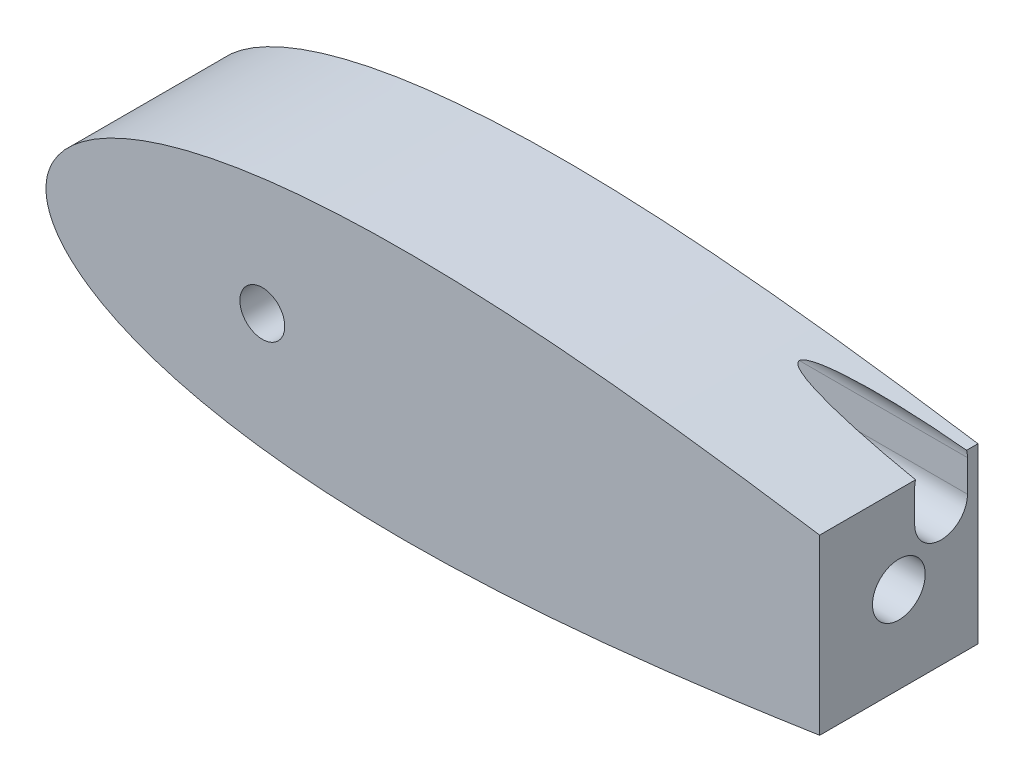
SolidWorks part; units mm, degrees
ref_plane "Front Plane" through (0, 0, 0) normal (0, 0, 1) x (1, 0, 0)
ref_plane "Top Plane" through (0, 0, 0) normal (0, 1, 0) x (1, 0, 0)
ref_plane "Right Plane" through (0, 0, 0) normal (1, 0, 0) x (0, 0, -1)
sketch "Sketch1" plane through (0, 0, 0) normal (0, 0, 1) x (1, 0, 0)
  line L0 (100, 0) -> (0, 0) construction
  line L1 (1.2169, -991.9959) -> (1.2169, 49008.0041) construction
  line L2 (93.345, 0) -> (114.935, 0) construction
  line L3 (125.634, 0) -> (131.6629, 0) construction
  line L4 (643.5991, 0) -> (643.5991, -1.016)
  line L9 (0, 0) -> (643.9668, 0)
  line L13 (460.661, 0) -> (473.361, 0)
  circle A0 centre (104.14, 0) radius 10.795 construction
  arc A1 (1.2169, -4.6585) -> (1.2169, 4.6585) centre (9.525, 0) cw
  arc A2 (641.5671, 0) -> (644.1071, 0) centre (642.8371, 0) ccw
  circle A4 centre (104.14, 0) radius 10.795
  circle A9 centre (40.64, 0) radius 12.7
  circle A14 centre (642.3793, 0) radius 1.5875 construction
  arc A15 (642.5108, -1.582) -> (642.5108, 1.582) centre (642.3793, 0) ccw
  spline S2 degree 3 poles (666.3448, -0.0547) (672.2538, 0) (666.3448, 0.0547) (662.8509, 0.2344) (656.505, 0.5436) (649.293, 1.0348) (640.4916, 1.7319) (630.4138, 2.6634) (619.0141, 3.8493) (606.375, 5.3044) (592.5439, 7.0376) (577.5855, 9.0506) (561.5643, 11.3389) (544.5497, 13.8907) (526.6141, 16.6877) (507.8326, 19.7051) (488.2827, 22.9117) (468.0444, 26.2704) (447.1994, 29.739) (425.8316, 33.2703) (404.0263, 36.8132) (381.8707, 40.3133) (359.4533, 43.7135) (336.8645, 46.9554) (314.1962, 49.9798) (291.5418, 52.7277) (268.9963, 55.1412) (246.6566, 57.1646) (224.6209, 58.7452) (202.9892, 59.8341) (181.8631, 60.3875) (161.3458, 60.367) (141.542, 59.7399) (122.5581, 58.4818) (104.5023, 56.5743) (87.485, 54.0089) (71.6197, 50.7848) (57.0237, 46.9125) (43.8205, 42.415) (32.1416, 37.3322) (22.1291, 31.7315) (13.9324, 25.7264) (7.6896, 19.5132) (3.4631, 13.4204) (1.1063, 7.9234) (0.1546, 3.5138) (-0.0622, 0) (0.1546, -3.5138) (1.1063, -7.9234) (3.4631, -13.4204) (7.6896, -19.5132) (13.9324, -25.7264) (22.1291, -31.7315) (32.1416, -37.3322) (43.8205, -42.415) (57.0237, -46.9125) (71.6197, -50.7848) (87.485, -54.0089) (104.5023, -56.5743) (122.5581, -58.4818) (141.542, -59.7399) (161.3458, -60.367) (181.8631, -60.3875) (202.9892, -59.8341) (224.6209, -58.7452) (246.6566, -57.1646) (268.9963, -55.1412) (291.5418, -52.7277) (314.1962, -49.9798) (336.8645, -46.9554) (359.4533, -43.7135) (381.8707, -40.3133) (404.0263, -36.8132) (425.8316, -33.2703) (447.1994, -29.739) (468.0444, -26.2704) (488.2827, -22.9117) (507.8326, -19.7051) (526.6141, -16.6877) (544.5497, -13.8907) (561.5643, -11.3389) (577.5855, -9.0506) (592.5439, -7.0376) (606.375, -5.3044) (619.0141, -3.8493) (630.4138, -2.6634) (640.4916, -1.7319) (649.293, -1.0348) (656.505, -0.5436) (662.8509, -0.2344) (666.3448, -0.0547) (672.2538, 0) (666.3448, 0.0547) knots -0.009667 -0.005395 -0.002168 0 0.002168 0.005395 0.009667 0.014967 0.021271 0.028553 0.036781 0.04592 0.055932 0.066773 0.078397 0.090755 0.103793 0.117456 0.131686 0.146422 0.1616 0.177156 0.193024 0.209135 0.225421 0.241812 0.258238 0.274629 0.290914 0.307025 0.322893 0.338448 0.353626 0.368361 0.38259 0.396253 0.40929 0.421647 0.43327 0.444109 0.454119 0.463255 0.471479 0.478755 0.485052 0.490344 0.49461 0.497833 0.5 0.502167 0.50539 0.509656 0.514948 0.521245 0.528521 0.536745 0.545881 0.555891 0.56673 0.578353 0.59071 0.603747 0.61741 0.631639 0.646374 0.661552 0.677107 0.692975 0.709086 0.725371 0.741762 0.758188 0.774579 0.790865 0.806976 0.822844 0.8384 0.853578 0.868314 0.882544 0.896207 0.909245 0.921603 0.933227 0.944068 0.95408 0.963219 0.971447 0.978729 0.985033 0.990333 0.994605 0.997832 1 1.002168 1.005395 1.009667 only from (670.56, 0) to (670.56, 0)
  point P2 (167.64, 0)
  point P8 (1.2169, -4.6585)
  point P10 (1.2169, 4.6585)
  point P28 (133.9182, 0)
  point P49 (130.0977, 0)
  point P59 (95.1064, 0)
  dimension "D2" = 21.59
  dimension "D3" = 1.016
  dimension "D4" = 1.27
  dimension "D8" = 25.4
  dimension "D9" = 63.5
  dimension "D10" = 3.175
  dimension "D6" = 63.5
extrude "Boss-Extrude1" add sketch "Sketch1" along normal blind 76.2 contours S2
sketch "Sketch3" plane through (0, 0, 76.2) normal (0, 0, 1) x (1, 0, 0)
  circle A0 centre (104.1392, 0) radius 10.795
  dimension "D1" = 21.59
extrude "Cut-Extrude2" cut sketch "Sketch3" against normal blind 76.2
sketch "Sketch4" plane through (0, 0, 76.2) normal (0, 0, 1) x (1, 0, 0)
sketch "Sketch6" plane through (0, 0, 0) normal (1, 0, 0) x (0, 0, -1)
  circle A0 centre (-20.32, 0) radius 6.35
  dimension "D1" = 12.7
  dimension "D2" = 20.32
extrude "Cut-Extrude3" cut sketch "Sketch6" against normal blind 0.0003 and the other way blind 53.34
sketch "Sketch7" plane through (0, 0, 0) normal (0, 0, -1) x (-1, 0, 0)
  circle A0 centre (-38.1, 0) radius 1.5875
  circle A1 centre (-50.8, 0) radius 1.5875
  dimension "D1" = 3.175
  dimension "D2" = 3.175
  dimension "D3" = 12.7
  dimension "D4" = 38.1
extrude "Cut-Extrude4" cut sketch "Sketch7" against normal blind 30.48
sketch "Sketch8" plane through (0, 0, 0) normal (0, 0, -1) x (-1, 0, 0)
  line L1 (-677.2433, 63.9901) -> (-372.4433, 63.9901)
  line L2 (-677.2433, 63.9901) -> (-677.2433, -63.0099)
  line L3 (-677.2433, -63.0099) -> (-372.4433, -63.0099)
  line L4 (-372.4433, 63.9901) -> (-372.4433, -63.0099)
  dimension "D1" = 127
  dimension "D2" = 372.4433
  dimension "D3" = 304.8
extrude "Cut-Extrude5" cut sketch "Sketch8" against normal blind 76.2
sketch "Sketch9" plane through (372.4433, 0, 0) normal (1, 0, 0) x (0, 0, -1)
  line L0 (0, -41.7363) -> (0, 41.7363) construction
  circle A0 centre (-38.1, 0) radius 12.7
  dimension "D1" = 25.4
  dimension "D2" = 38.1
extrude "Cut-Extrude6" cut sketch "Sketch9" against normal blind 101.6 contours A0
sketch "Sketch10" plane through (0, 0, 0) normal (0, 0, -1) x (-1, 0, 0)
  line L0 (-372.4433, -41.7363) -> (-372.4433, 41.7363) construction
  circle A0 centre (-343.8683, 0) radius 3.175
  circle A1 centre (-286.7183, 0) radius 3.175
  dimension "D1" = 57.15
  dimension "D2" = 28.575
  dimension "D3" = 6.35
  dimension "D4" = 6.35
extrude "Cut-Extrude7" cut sketch "Sketch10" against normal blind 57.15
sketch "Sketch11" plane through (0, 0, 0) normal (0, 0, -1) x (-1, 0, 0)
  circle A0 centre (-286.7183, 0) radius 5.08
  circle A1 centre (-343.8683, 0) radius 5.08
  dimension "D1" = 10.16
extrude "Cut-Extrude8" cut sketch "Sketch11" against normal blind 6.35
sketch "Sketch12" plane through (0, 0, 0) normal (0, 0, -1) x (-1, 0, 0)
  circle A0 centre (-38.1, 0) radius 3.175
  circle A1 centre (-50.8, 0) radius 3.175
  dimension "D1" = 6.35
  dimension "D2" = 6.35
extrude "Cut-Extrude9" cut sketch "Sketch12" against normal blind 6.35
sketch "Sketch13" plane through (372.4433, 0, 0) normal (1, 0, 0) x (0, 0, -1)
  line L0 (-17.78, 23.2323) -> (-17.78, 38.4723) construction
  line L1 (-30.48, 23.2323) -> (-30.48, 38.4723)
  line L2 (-5.08, 23.2323) -> (-5.08, 38.4723)
  line L3 (0, -41.7363) -> (0, 41.7363) construction
  line L4 (-76.2, -41.7363) -> (-76.2, 41.7363) construction
  arc A0 (-30.48, 23.2323) -> (-5.08, 23.2323) centre (-17.78, 23.2323) ccw
  arc A1 (-5.08, 38.4723) -> (-30.48, 38.4723) centre (-17.78, 38.4723) ccw
  point P2 (-17.78, 30.8523)
  dimension "D1" = 5.08
  dimension "D2" = 45.72
  dimension "D4" = 15.24
extrude "Cut-Extrude10" cut sketch "Sketch13" against normal blind 198.458
sketch "Sketch15" plane through (0, 0, 0) normal (0, 0, -1) x (-1, 0, 0)
  line L0 (-372.4433, -41.7363) -> (-372.4433, 41.7363) construction
  line L1 (-261.3613, -30.48) -> (-173.9853, -30.48)
  line L2 (-261.3613, -30.48) -> (-261.3613, 30.48)
  line L3 (-261.3613, 30.48) -> (-173.9853, 30.48)
  line L4 (-173.9853, -30.48) -> (-173.9853, 30.48)
  point P4 (0, 0)
  point P5 (0, 0)
  point P6 (0, 0)
  point P7 (0, 0)
  dimension "D1" = 87.376
  dimension "D2" = 60.96
  dimension "D3" = 111.082
extrude "Cut-Extrude11" cut sketch "Sketch15" against normal blind 33.3
